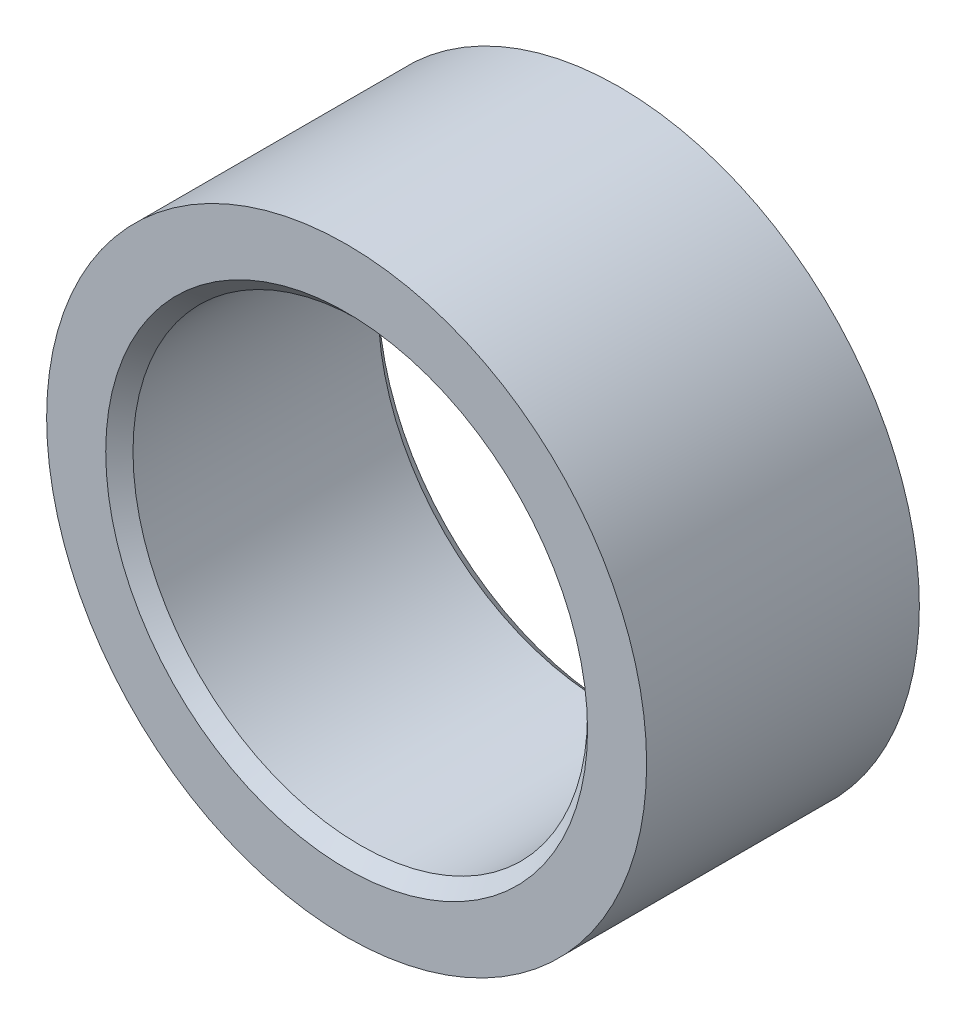
SolidWorks part; units mm, degrees
material "Cast Alloy Steel"
ref_plane "Front Plane" through (0, 0, 0) normal (0, 0, 1) x (1, 0, 0)
ref_plane "Top Plane" through (0, 0, 0) normal (0, 1, 0) x (1, 0, 0)
ref_plane "Right Plane" through (0, 0, 0) normal (1, 0, 0) x (0, 0, -1)
sketch "Sketch1" plane through (0, 0, 0) normal (0, 0, 1) x (1, 0, 0)
  circle A0 centre (0, 0) radius 5
  circle A1 centre (0, 0) radius 6.6
  dimension "D1" = 10
  dimension "D2" = 1.6
extrude "Boss-Extrude1" add sketch "Sketch1" along normal mid plane 6
chamfer "Chamfer1" distance 0.3 angle 45 2 edges at (5, 0, -3) (5, 0, 3)
